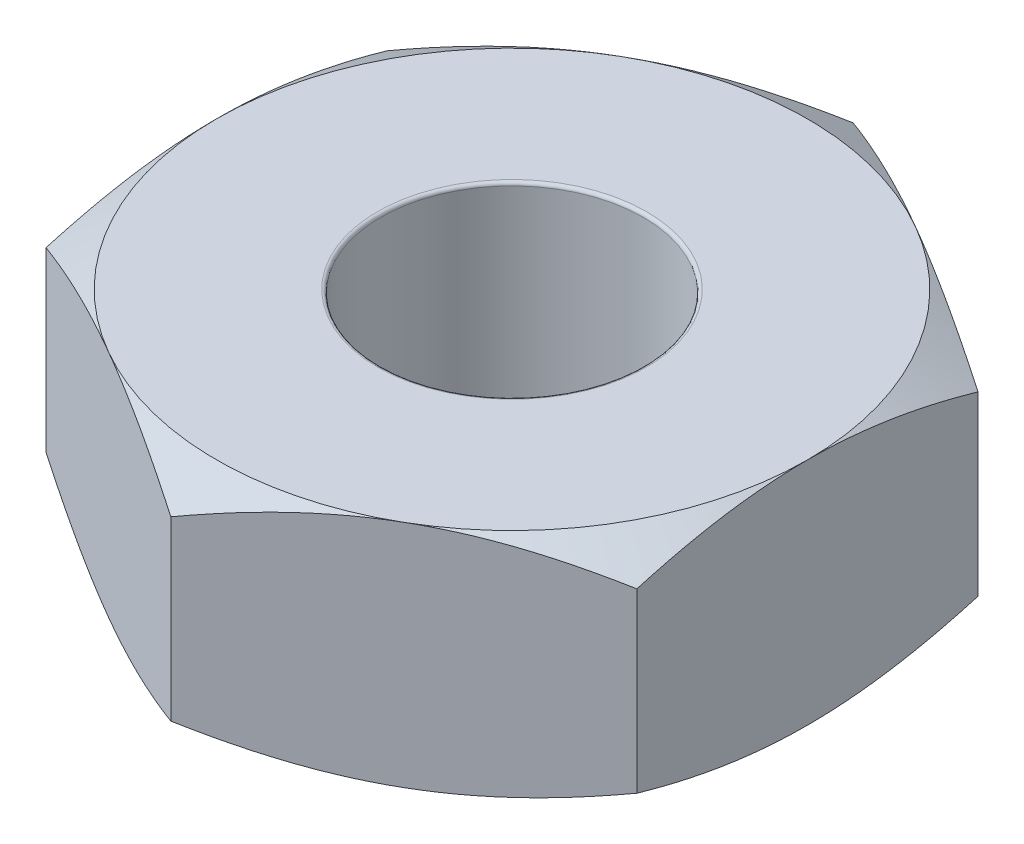
SolidWorks part; units mm, degrees
ref_plane "Front Plane" through (0, 0, 0) normal (0, 0, 1) x (1, 0, 0)
ref_plane "Top Plane" through (0, 0, 0) normal (0, 1, 0) x (1, 0, 0)
ref_plane "Right Plane" through (0, 0, 0) normal (1, 0, 0) x (0, 0, -1)
sketch "Sketch1" plane through (0, 0, 0) normal (0, 1, 0) x (1, 0, 0)
  line L1 (2.25, -1.299) -> (2.25, 1.299)
  line L2 (2.25, 1.299) -> (0, 2.5981)
  line L3 (0, 2.5981) -> (-2.25, 1.299)
  line L4 (-2.25, 1.299) -> (-2.25, -1.299)
  line L5 (-2.25, -1.299) -> (0, -2.5981)
  line L6 (0, -2.5981) -> (2.25, -1.299)
  circle A0 centre (0, 0) radius 1
  circle A1 centre (0, 0) radius 2.25 construction
  point P3 (0, 0)
  point P11 (0, 0)
  dimension "D1" = 2
  dimension "D2" = 4.5
extrude "Boss-Extrude1" add sketch "Sketch1" along normal blind 1.75
sketch "Sketch2" plane through (0, 1.75, 0) normal (0, 1, 0) x (1, 0, 0)
  circle A0 centre (0, 0) radius 2.25 construction
  circle A1 centre (0, 0) radius 2.25
extrude "Cut-Extrude1" cut sketch "Sketch2" against normal blind 1.75 draft 60 flip side to cut
sketch "Sketch3" plane through (0, 0, 0) normal (0, -1, 0) x (1, 0, 0)
  circle A0 centre (0, 0) radius 2.25 construction
  circle A1 centre (0, 0) radius 2.25
extrude "Cut-Extrude3" cut sketch "Sketch3" against normal blind 1.75 draft 60 flip side to cut
fillet "Fillet1" radius 0.025 2 edges at (0, 0, 1) (0, 1.75, 1)
